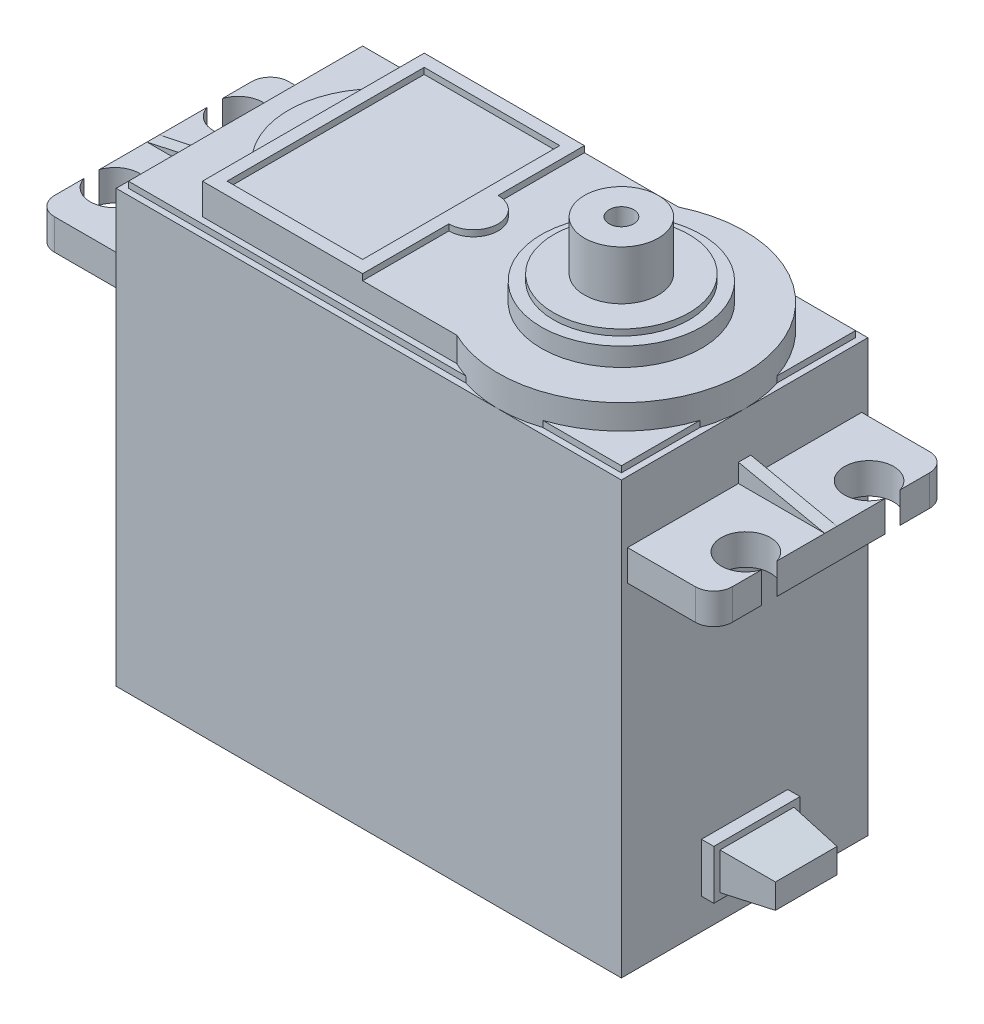
SolidWorks part; units mm, degrees
ref_plane "Front Plane" through (0, 0, 0) normal (0, 0, 1) x (1, 0, 0)
ref_plane "Top Plane" through (0, 0, 0) normal (0, 1, 0) x (1, 0, 0)
ref_plane "Right Plane" through (0, 0, 0) normal (1, 0, 0) x (0, 0, -1)
sketch "Sketch1" plane through (0, 0, 0) normal (0, 1, 0) x (1, 0, 0)
  line L1 (-20.5, -10) -> (20.5, -10)
  line L2 (-20.5, -10) -> (-20.5, 10)
  line L3 (-20.5, 10) -> (20.5, 10)
  line L4 (20.5, -10) -> (20.5, 10)
  line L5 (-20.5, -10) -> (20.5, 10) construction
  line L6 (-20.5, 10) -> (20.5, -10) construction
  point P0 (0, 0)
  dimension "D1" = 41
  dimension "D2" = 20
extrude "Boss-Extrude1" add sketch "Sketch1" along normal blind 40
chamfer "Chamfer1" distance 2 angle 45 4 edges at (20.5, 0, 0) (0, 0, -10) (-20.5, 0, 0) (0, 0, 10)
sketch "Sketch2" plane through (0, 0, 0) normal (0, -1, 0) x (1, 0, 0)
  line L0 (-20.5, 10) -> (20.5, 10) construction
  line L1 (20.5, 10) -> (20.5, -10) construction
  line L2 (20.5, -10) -> (-20.5, -10) construction
  line L3 (-20.5, -10) -> (-20.5, 10) construction
  circle A0 centre (18.25, 7.75) radius 2.25
  circle A1 centre (-18.25, 7.75) radius 2.25
  circle A2 centre (-18.25, -7.75) radius 2.25
  circle A3 centre (18.25, -7.75) radius 2.25
  dimension "D1" = 4.5
  dimension "D2" = 4.5
  dimension "D3" = 4.5
  dimension "D4" = 4.5
extrude "Cut-Extrude1" cut sketch "Sketch2" against normal blind 1
sketch "Sketch3" plane through (20.5, 0, 0) normal (1, 0, 0) x (0, 0, -1)
  line L0 (-10, 40) -> (-10, 2) construction
  line L1 (-9.5, 32) -> (9.5, 32)
  line L2 (-9.5, 32) -> (-9.5, 29.5)
  line L3 (-9.5, 29.5) -> (9.5, 29.5)
  line L4 (9.5, 32) -> (9.5, 29.5)
  line L5 (-10, 40) -> (10, 40) construction
  dimension "D1" = 19
  dimension "D2" = 0.5
  dimension "D3" = 2.5
  dimension "D4" = 8
extrude "Boss-Extrude2" add sketch "Sketch3" along normal blind 7
fillet "Fillet1" radius 1.5 2 edges at (27.5, 30.75, -9.5) (27.5, 30.75, 9.5)
sketch "Sketch4" plane through (0, 32, 0) normal (0, 1, 0) x (1, 0, 0)
  line L0 (20.5, -10) -> (20.5, 10) construction
  line L1 (20.5, 0.5) -> (27.5, 0.5)
  line L2 (20.5, 0.5) -> (20.5, -0.5)
  line L3 (20.5, -0.5) -> (27.5, -0.5)
  line L4 (27.5, 0.5) -> (27.5, -0.5)
  line L5 (27.5, 8) -> (27.5, -8) construction
  line L6 (26, 9.5) -> (20.5, 9.5) construction
  dimension "D1" = 1
  dimension "D2" = 9
extrude "Boss-Extrude3" add sketch "Sketch4" along normal blind 1.5
sketch "Sketch5" plane through (0, 0, 0.5) normal (0, 0, 1) x (1, 0, 0)
  line L0 (27.5, 33.5) -> (27.5, 32) construction
  line L1 (20.5, 33.5) -> (27.5, 33.5) construction
  line L2 (27.5, 33.5) -> (27.5, 32)
  line L3 (20.5, 33.5) -> (27.5, 33.5)
  line L4 (20.5, 33.5) -> (27.5, 32)
extrude "Cut-Extrude2" cut sketch "Sketch5" against normal blind 1
sketch "Sketch6" plane through (0, 32, 0) normal (0, 1, 0) x (1, 0, 0)
  line L2 (27.5, 8) -> (27.5, 0.5) construction
  line L3 (27.5, -0.5) -> (27.5, -8) construction
  line L4 (26, 9.5) -> (20.5, 9.5) construction
  line L5 (26, -9.5) -> (20.5, -9.5) construction
  circle A0 centre (25.6, 5) radius 2
  circle A1 centre (25.6, -5) radius 2
  dimension "D1" = 4
  dimension "D2" = 4
  dimension "D3" = 1.9
  dimension "D4" = 1.9
  dimension "D5" = 4.5
  dimension "D6" = 4.5
extrude "Cut-Extrude3" cut sketch "Sketch6" against normal blind 2.5
mirror "Mirror1" about plane through (0, 0, 0) normal (1, 0, 0) of "Boss-Extrude2", "Fillet1", "Boss-Extrude3", "Cut-Extrude2", "Cut-Extrude3"
sketch "Sketch7" plane through (0, 40, 0) normal (0, 1, 0) x (1, 0, 0)
  line L0 (20.5, 10) -> (-20.5, 10) construction
  line L1 (20.5, -10) -> (20.5, 10) construction
  line L2 (-20.5, -10) -> (20.5, -10) construction
  line L3 (-20.5, 10) -> (-20.5, -10) construction
  line L4 (20.5, 10) -> (-20.5, 10)
  line L5 (20.5, -10) -> (20.5, 10)
  line L6 (-20.5, -10) -> (20.5, -10)
  line L7 (-20.5, 10) -> (-20.5, -10)
extrude "Cut-Extrude4" cut sketch "Sketch7" against normal blind 3
sketch "Sketch8" plane through (0, 37, 0) normal (0, 1, 0) x (1, 0, 0)
  line L0 (20.5, 10) -> (-20.5, 10) construction
  line L1 (-20, -9.5) -> (20, -9.5)
  line L2 (-20, -9.5) -> (-20, 9.5)
  line L3 (-20, 9.5) -> (20, 9.5)
  line L4 (20, -9.5) -> (20, 9.5)
  line L5 (-20, -9.5) -> (20, 9.5) construction
  line L6 (-20, 9.5) -> (20, -9.5) construction
  line L7 (20.5, -0.5) -> (20.5, -9.5) construction
  point P0 (0, 0)
  dimension "D1" = 0.5
  dimension "D2" = 0.5
extrude "Boss-Extrude4" add sketch "Sketch8" along normal blind 0.5
sketch "Sketch9" plane through (0, 37, 0) normal (0, 1, 0) x (1, 0, 0)
  line L0 (20.5, 10) -> (-20.5, 10) construction
  line L1 (20.5, 9.5) -> (20.5, 0.5) construction
  line L2 (6.1411, 9) -> (-14.5, 9)
  line L3 (-14.5, 9) -> (-14.5, 5)
  line L4 (-14.5, -9) -> (6.1411, -9)
  line L5 (-20.5, -10) -> (20.5, -10) construction
  line L6 (-20.5, 9.5) -> (-20.5, 0.5) construction
  line L7 (-14.5, -5) -> (-14.5, -9)
  arc A0 (6.1411, -9) -> (6.1411, 9) centre (10.5, 0) ccw
  arc A1 (-14.5, 5) -> (-14.5, -5) centre (-9.25, 0) ccw
  point P15 (-16.5, 0)
  point P16 (-14.5, 5)
  point P17 (-14.5, -5)
  dimension "D1" = 20
  dimension "D5" = 2
  dimension "D2" = 1
  dimension "D3" = 1
  dimension "D4" = 6
  dimension "D6" = 10
extrude "Boss-Extrude6" add sketch "Sketch9" along normal blind 2.5
sketch "Sketch10" plane through (0, 39.5, 0) normal (0, 1, 0) x (1, 0, 0)
  line L0 (6.1411, 9) -> (-14.5, 9) construction
  line L1 (-14.5, 9) -> (-1.5, 9)
  line L2 (-14.5, 9) -> (-14.5, -9)
  line L3 (-14.5, -9) -> (-1.5, -9)
  line L4 (-1.5, 9) -> (-1.5, 2)
  line L5 (-14.5, -9) -> (6.1411, -9) construction
  line L6 (-14.5, 9) -> (-14.5, 5) construction
  line L7 (-1.5, -2) -> (-1.5, -9)
  line L9 (-13.5, 8) -> (-2.5, 8)
  line L10 (-13.5, 8) -> (-13.5, -8)
  line L11 (-13.5, -8) -> (-2.5, -8)
  line L12 (-2.5, 8) -> (-2.5, -8)
  arc A0 (-1.5, -2) -> (-1.5, 2) centre (-1.5, 0) ccw
  dimension "D5" = 4
  dimension "D1" = 13
  dimension "D2" = 0
  dimension "D3" = 0
  dimension "D4" = 0
  dimension "D6" = 1
  dimension "D7" = 1
  dimension "D8" = 1
  dimension "D9" = 1
extrude "Boss-Extrude7" add sketch "Sketch10" along normal blind 0.5
sketch "Sketch11" plane through (0, 39.5, 0) normal (0, 1, 0) x (1, 0, 0)
  circle A0 centre (10.5, 0) radius 6.5
  dimension "D1" = 13
extrude "Boss-Extrude8" add sketch "Sketch11" along normal blind 1.5
sketch "Sketch12" plane through (0, 41, 0) normal (0, 1, 0) x (1, 0, 0)
  circle A0 centre (10.5, 0) radius 5.5
  dimension "D1" = 11
extrude "Boss-Extrude9" add sketch "Sketch12" along normal blind 0.5
sketch "Sketch13" plane through (0, 41.5, 0) normal (0, 1, 0) x (1, 0, 0)
  circle A0 centre (10.5, 0) radius 3
  dimension "D1" = 6
extrude "Boss-Extrude10" add sketch "Sketch13" along normal blind 4
sketch "Sketch14" plane through (0, 45.5, 0) normal (0, 1, 0) x (1, 0, 0)
  circle A0 centre (10.5, 0) radius 1
  dimension "D1" = 2
extrude "Cut-Extrude5" cut sketch "Sketch14" against normal blind 8
sketch "Sketch15" plane through (20.5, 0, 0) normal (1, 0, 0) x (0, 0, -1)
  line L0 (5.5139, 0) -> (-5.5139, 0) construction
  line L1 (-3.5, 8.5) -> (3.5, 8.5)
  line L2 (-3.5, 8.5) -> (-3.5, 4.5)
  line L3 (-3.5, 4.5) -> (3.5, 4.5)
  line L4 (3.5, 8.5) -> (3.5, 4.5)
  line L5 (-10, 37) -> (-10, 2) construction
  dimension "D1" = 4.5
  dimension "D2" = 7
  dimension "D3" = 4
  dimension "D4" = 6.5
extrude "Boss-Extrude11" add sketch "Sketch15" along normal blind 5
sketch "Sketch16" plane through (25.5, 0, 0) normal (1, 0, 0) x (0, 0, -1)
  line L0 (3.5, 8.5) -> (-3.5, 8.5) construction
  line L1 (-3, 8) -> (3, 8)
  line L2 (-3, 8) -> (-3, 5)
  line L3 (-3, 5) -> (3, 5)
  line L4 (3, 8) -> (3, 5)
  line L5 (-3.5, 4.5) -> (3.5, 4.5) construction
  line L6 (3.5, 4.5) -> (3.5, 8.5) construction
  line L7 (-3.5, 8.5) -> (-3.5, 4.5) construction
  line L8 (-3.5, 8.5) -> (-3.5, 4.5) construction
  line L9 (3.5, 8.5) -> (-3.5, 8.5) construction
  line L10 (-3.5, 8.5) -> (-3.5, 4.5)
  line L11 (-3.5, 4.5) -> (3.5, 4.5)
  line L12 (3.5, 4.5) -> (3.5, 8.5)
  line L13 (3.5, 8.5) -> (-3.5, 8.5)
  dimension "D1" = 0.5
  dimension "D2" = 0.5
  dimension "D3" = 0.5
  dimension "D4" = 0.5
extrude "Cut-Extrude6" cut sketch "Sketch16" against normal blind 4
sketch "Sketch17" plane through (0, 5, 0) normal (0, -1, 0) x (1, 0, 0)
  line L0 (21.5, 3) -> (25.5, 2.5)
  line L1 (25.5, 3) -> (25.5, -3) construction
  line L2 (21.5, -3) -> (25.5, -2.5)
  line L3 (21.5, -3) -> (25.5, -3) construction
  line L4 (21.5, 3) -> (25.5, 3) construction
  line L5 (21.5, -3) -> (25.5, -3)
  line L6 (25.5, 3) -> (25.5, 2.5)
  line L7 (21.5, 3) -> (25.5, 3)
  line L8 (25.5, -2.5) -> (25.5, -3)
  dimension "D1" = 0.5
  dimension "D2" = 0.5
extrude "Cut-Extrude7" cut sketch "Sketch17" against normal blind 3
sketch "Sketch18" plane through (0, 0, -3.5) normal (0, 0, -1) x (-1, 0, 0)
  line L0 (-21.5, 8) -> (-25.5, 8)
  line L1 (-25.5, 8) -> (-25.5, 7.5)
  line L2 (-25.5, 8) -> (-25.5, 5) construction
  line L3 (-25.5, 7.5) -> (-21.5, 8)
  line L4 (-21.5, 5) -> (-25.5, 5)
  line L5 (-25.5, 5) -> (-25.5, 5.5)
  line L6 (-25.5, 5.5) -> (-21.5, 5)
  dimension "D1" = 0.5
  dimension "D2" = 0.5
extrude "Cut-Extrude8" cut sketch "Sketch18" against normal blind 7
